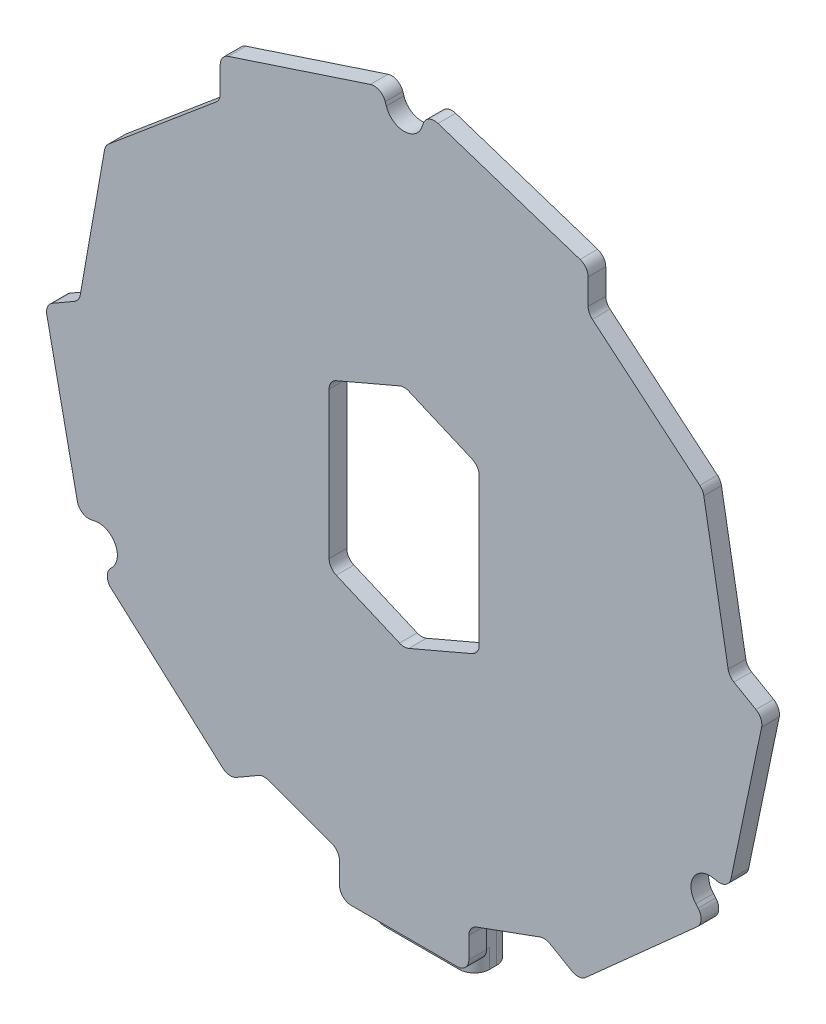
SolidWorks part; units mm, degrees
ref_plane "Front Plane" through (0, 0, 0) normal (0, 0, 1) x (1, 0, 0)
ref_plane "Top Plane" through (0, 0, 0) normal (0, 1, 0) x (1, 0, 0)
ref_plane "Right Plane" through (0, 0, 0) normal (1, 0, 0) x (0, 0, -1)
sketch "Sketch1" plane through (0, 0, 0) normal (0, 0, 1) x (1, 0, 0)
  line L0 (7.3627, 62.7062) -> (-2.4088, 54.5069)
  line L1 (-2.4088, 54.5069) -> (-4.6238, 41.9449)
  line L2 (-4.6238, 41.9449) -> (-7.5304, 40.2668)
  line L3 (-7.5304, 40.2668) -> (-4.1657, 24.153)
  line L4 (-4.1657, 24.153) -> (8.1068, 13.1822)
  line L5 (8.1068, 13.1822) -> (11.0134, 14.8604)
  line L6 (11.0134, 14.8604) -> (17.5, 12.4994)
  line L7 (17.5, 12.4994) -> (17.5, 9)
  line L8 (17.5, 9) -> (28.5, 9)
  line L9 (28.5, 9) -> (28.5, 12.4994)
  line L10 (28.5, 12.4994) -> (34.9866, 14.8604)
  line L11 (34.9866, 14.8604) -> (37.8932, 13.1822)
  line L12 (37.8932, 13.1822) -> (50.1657, 24.153)
  line L13 (50.1657, 24.153) -> (53.5304, 40.2668)
  line L14 (53.5304, 40.2668) -> (50.6238, 41.9449)
  line L15 (50.6238, 41.9449) -> (48.4088, 54.5069)
  line L16 (48.4088, 54.5069) -> (38.6373, 62.7062)
  line L17 (38.6373, 62.7062) -> (38.6373, 66.0625)
  line L18 (38.6373, 66.0625) -> (23, 71.2054)
  line L19 (23, 71.2054) -> (7.3627, 66.0625)
  line L20 (7.3627, 66.0625) -> (7.3627, 62.7062)
  line L21 (52.4449, 22.8372) -> (56.3475, 41.5271) construction
  line L22 (38.2103, 10.1124) -> (52.4449, 22.8372) construction
  line L23 (34.7462, 12.1124) -> (38.2103, 10.1124) construction
  line L24 (56.3475, 41.5271) -> (52.8834, 43.5271) construction
  line L25 (52.8834, 43.5271) -> (50.7128, 55.8372) construction
  line L26 (30.5, 10.5669) -> (34.7462, 12.1124) construction
  line L27 (11.2538, 12.1124) -> (15.5, 10.5669) construction
  line L28 (7.7897, 10.1124) -> (11.2538, 12.1124) construction
  line L29 (-6.4449, 22.8372) -> (7.7897, 10.1124) construction
  line L30 (-10.3475, 41.5271) -> (-6.4449, 22.8372) construction
  line L31 (-6.8834, 43.5271) -> (-10.3475, 41.5271) construction
  line L32 (50.7128, 55.8372) -> (41.1373, 63.872) construction
  line L33 (41.1373, 67.872) -> (23, 73.8372) construction
  line L34 (23, 73.8372) -> (4.8627, 67.872) construction
  line L35 (4.8627, 63.872) -> (-4.7128, 55.8372) construction
  line L36 (-4.7128, 55.8372) -> (-6.8834, 43.5271) construction
  line L38 (41.1373, 63.872) -> (41.1373, 67.872) construction
  line L39 (4.8627, 67.872) -> (4.8627, 63.872) construction
  line L40 (23, 49.4723) -> (16.6184, 46.7373)
  line L41 (16.6184, 46.7373) -> (16.6184, 32.937)
  line L42 (16.6184, 32.937) -> (23, 30.202)
  line L43 (23, 30.202) -> (29.3816, 32.937)
  line L44 (29.3816, 32.937) -> (29.3816, 46.7373)
  line L45 (29.3816, 46.7373) -> (23, 49.4723)
  line L47 (23, 47.2964) -> (18.6184, 45.4185) construction
  line L48 (27.3816, 45.4185) -> (23, 47.2964) construction
  line L49 (27.3816, 34.2558) -> (27.3816, 45.4185) construction
  line L50 (23, 32.378) -> (27.3816, 34.2558) construction
  line L51 (18.6184, 34.2558) -> (23, 32.378) construction
  line L52 (18.6184, 45.4185) -> (18.6184, 34.2558) construction
  line L53 (15.5, 0) -> (30.5, 0) construction
  line L54 (15.5, 10.5669) -> (15.5, 0) construction
  line L55 (30.5, 0) -> (30.5, 10.5669) construction
  dimension "D1" = 2.5
  dimension "D2" = 2.5
  dimension "D3" = 2.5
  dimension "D4" = 2.5
  dimension "D5" = 2.5
  dimension "D6" = 2.5
  dimension "D10" = 2.5
  dimension "D9" = 2.5
  dimension "D11" = 2.5
  dimension "D12" = 2.5
  dimension "D13" = 2.5
  dimension "D14" = 2.5
  dimension "D16" = 2.5
  dimension "D15" = 2.5
  dimension "D17" = 2.5
  dimension "D18" = 2.5
  dimension "D19" = 2.5
  dimension "D20" = 2.5
  dimension "D21" = 2
  dimension "D22" = 2
  dimension "D23" = 2
  dimension "D24" = 2
  dimension "D25" = 2
  dimension "D26" = 2
  dimension "D27" = 9
  dimension "D7" = 2
  dimension "D8" = 2
extrude "Boss-Extrude1" add sketch "Sketch1" along normal blind 1.5
sketch "Sketch2" plane through (0, 0, 1.5) normal (0, 0, 1) x (1, 0, 0)
  line L0 (-4.5801, 26.1377) -> (-3.3078, 26.4034)
  line L1 (-7.5304, 40.2668) -> (-4.1657, 24.153) construction
  line L2 (-2.6541, 22.8018) -> (-1.7879, 23.7708)
  line L3 (-4.1657, 24.153) -> (8.1068, 13.1822) construction
  line L4 (-4.5801, 26.1377) -> (-4.1657, 24.153)
  line L5 (-4.1657, 24.153) -> (-2.6541, 22.8018)
  arc A0 (-1.7879, 23.7708) -> (-3.3078, 26.4034) centre (-2.9808, 24.8372) ccw
  circle A1 centre (-2.9808, 24.8372) radius 1.44 construction
  dimension "D1" = 1.6
extrude "Cut-Extrude1" cut sketch "Sketch2" against normal through all
pattern_circular "CirPattern1" count 3 over 360 about axis through (23, 39.8372, 0) along (0, 0, 1) of "Cut-Extrude1"
fillet "Fillet1" radius 1 30 edges at (-2.6541, 22.8018, 0.75) (-4.5801, 26.1377, 0.75) (-7.5304, 40.2668, 0.75) (-4.6238, 41.9449, 0.75) (-2.4088, 54.5069, 0.75) (7.3627, 62.7062, 0.75) (7.3627, 66.0625, 0.75) (21.074, 70.572, 0.75) (24.926, 70.572, 0.75) (38.6373, 66.0625, 0.75) (38.6373, 62.7062, 0.75) (48.4088, 54.5069, 0.75) (50.6238, 41.9449, 0.75) (53.5304, 40.2668, 0.75) (50.5801, 26.1377, 0.75) (48.6541, 22.8018, 0.75) (37.8932, 13.1822, 0.75) (34.9866, 14.8604, 0.75) (28.5, 12.4994, 0.75) (28.5, 9, 0.75) (17.5, 9, 0.75) (17.5, 12.4994, 0.75) (8.1068, 13.1822, 0.75) (11.0134, 14.8604, 0.75) (29.3816, 32.937, 0.75) (29.3816, 46.7373, 0.75) (23, 30.202, 0.75) (16.6184, 32.937, 0.75) (23, 49.4723, 0.75) (16.6184, 46.7373, 0.75)
sketch "Sketch3" plane through (0, 0, 0) normal (0, 0, -1) x (-1, 0, 0)
  line L0 (-23, 49.3843) -> (-23, 30.29) construction
  line L1 (-29.3816, 39.8372) -> (-16.6184, 39.8372) construction
  line L2 (-29.3816, 33.5964) -> (-29.3816, 46.0779) construction
  line L3 (-16.6184, 46.0779) -> (-16.6184, 33.5964) construction
  arc A0 (-22.6061, 49.3035) -> (-23.3939, 49.3035) centre (-23, 48.3843) ccw construction
  arc A1 (-23.3939, 30.3709) -> (-22.6061, 30.3709) centre (-23, 31.29) ccw construction
  point P14 (-23, 39.8372)
sketch "Sketch4" plane through (0, 0, 0) normal (0, 0, -1) x (-1, 0, 0)
  line L0 (-27.47, 9) -> (-27.47, 7.38)
  line L1 (-18.5, 9) -> (-27.5, 9) construction
  line L2 (-27.47, 7.38) -> (-18.53, 7.38)
  line L3 (-18.53, 7.38) -> (-18.53, 9)
  line L4 (-18.53, 9) -> (-18.53, 16.55)
  line L5 (-18.53, 16.55) -> (-27.47, 16.55)
  line L6 (-27.47, 16.55) -> (-27.47, 9)
  line L7 (-23, 9) -> (-23, 16.55) construction
  dimension "D1" = 8.94
  dimension "D2" = 9.17
  dimension "D3" = 7.55
extrude "Boss-Extrude2" add sketch "Sketch4" along normal blind 3.17
fillet "Fillet2" radius 1.3 4 edges at (18.53, 11.965, -3.17) (27.47, 11.965, -3.17) (27.47, 8.19, 0) (18.53, 8.19, 0)
sketch "Sketch5" plane through (0, 0, 0) normal (0, 0, -1) x (-1, 0, 0)
  line L0 (-29.3816, 39.8372) -> (-16.6184, 39.8372) construction
  line L1 (-23, 49.3843) -> (-23, 30.29) construction
  circle A0 centre (-2.99, 46.9372) radius 2
  dimension "D1" = 4
  dimension "D2" = 7.1
  dimension "D3" = 20.01
extrude "Boss-Extrude3" add sketch "Sketch5" along normal blind 3.17
equation "\"Var01mm\"= 2.5mm"
equation "\"D1@Sketch1\"=\"Var01mm\""
equation "\"D2@Sketch1\"=\"Var01mm\""
equation "\"D20@Sketch1\"=\"Var01mm\""
equation "\"D19@Sketch1\"=\"Var01mm\""
equation "\"D18@Sketch1\"=\"Var01mm\""
equation "\"D17@Sketch1\"=\"Var01mm\""
equation "\"D15@Sketch1\"=\"Var01mm\""
equation "\"D16@Sketch1\"=\"Var01mm\""
equation "\"D14@Sketch1\"=\"Var01mm\""
equation "\"D13@Sketch1\"=\"Var01mm\""
equation "\"D12@Sketch1\"=\"Var01mm\""
equation "\"D11@Sketch1\"=\"Var01mm\""
equation "\"D9@Sketch1\"=\"Var01mm\""
equation "\"D10@Sketch1\"=\"Var01mm\""
equation "\"D6@Sketch1\"=\"Var01mm\""
equation "\"D5@Sketch1\"=\"Var01mm\""
equation "\"D4@Sketch1\"=\"Var01mm\""
equation "\"D3@Sketch1\"=\"Var01mm\""
equation "\"Var02\"=2"
equation "\"D21@Sketch1\"=\"Var02\""
equation "\"D22@Sketch1\"=\"Var02\""
equation "\"D23@Sketch1\"=\"Var02\""
equation "\"D24@Sketch1\"=\"Var02\""
equation "\"D25@Sketch1\"=\"Var02\""
equation "\"D26@Sketch1\"=\"Var02\""
